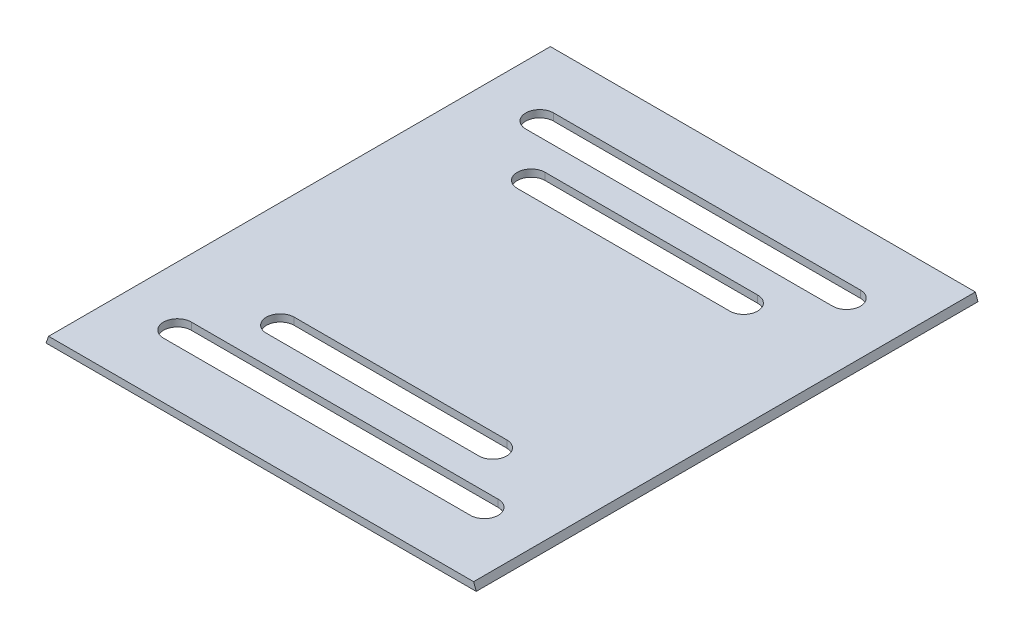
SolidWorks part; units mm, degrees
ref_plane "Front Plane" through (0, 0, 0) normal (0, 0, 1) x (1, 0, 0)
ref_plane "Top Plane" through (0, 0, 0) normal (0, 1, 0) x (1, 0, 0)
ref_plane "Right Plane" through (0, 0, 0) normal (1, 0, 0) x (0, 0, -1)
sketch "Sketch1" plane through (0, 0, 0) normal (0, 0, 1) x (1, 0, 0)
  line L3 (-79.7983, 0.2182) -> (-80.7023, -2.2654)
  line L4 (-80.7023, -2.2654) -> (73.6358, -2.2654)
  line L5 (73.6358, -2.2654) -> (72.7318, 0.2182)
  line L6 (-79.7983, 0.2182) -> (-79.7672, 0.3037)
  line L7 (-79.7672, 0.3037) -> (72.5419, 0.3037)
  line L8 (72.7318, 0.2182) -> (72.7007, 0.3037)
  line L9 (72.7007, 0.3037) -> (72.5419, 0.3037)
extrude "Boss-Extrude1" add sketch "Sketch1" against normal blind 180
sketch "Sketch2" plane through (0, 0.3037, 0) normal (0, 1, 0) x (1, 0, 0)
  line L0 (-3.5332, 180) -> (-3.5332, 0) construction
  line L1 (72.7007, 180) -> (-79.7672, 180) construction
  line L2 (72.7007, 0) -> (-79.7672, 0) construction
  line L3 (-79.7672, 90) -> (72.7007, 90) construction
  line L4 (-79.7672, 180) -> (-79.7672, 0) construction
  line L5 (72.7007, 180) -> (72.7007, 0) construction
  line L6 (-3.5332, 90) -> (-79.7672, 0) construction
  line L7 (-3.5332, 90) -> (72.7007, 0) construction
  line L8 (-41.6502, 50) -> (34.5837, 50)
  line L9 (-41.6502, 40) -> (34.5837, 40)
  line L10 (-56.9956, 30.0246) -> (51.5038, 30.0246)
  line L11 (-58.5703, 20.0246) -> (51.5038, 20.0246)
  line L12 (-56.9956, 30.0246) -> (-58.5703, 30.0246)
  line L13 (-56.9956, 149.9754) -> (-58.5703, 149.9754)
  line L14 (-58.5703, 159.9754) -> (51.5038, 159.9754)
  line L15 (-56.9956, 149.9754) -> (51.5038, 149.9754)
  line L16 (-41.6502, 140) -> (34.5837, 140)
  line L17 (-41.6502, 130) -> (34.5837, 130)
  arc A0 (-41.6502, 50) -> (-41.6502, 40) centre (-41.6502, 45) ccw
  arc A1 (34.5837, 40) -> (34.5837, 50) centre (34.5837, 45) ccw
  arc A2 (-58.5703, 30.0246) -> (-58.5703, 20.0246) centre (-58.5703, 25.0246) ccw
  arc A3 (51.5038, 20.0246) -> (51.5038, 30.0246) centre (51.5038, 25.0246) ccw
  arc A4 (51.5038, 159.9754) -> (51.5038, 149.9754) centre (51.5038, 154.9754) cw
  arc A5 (-58.5703, 149.9754) -> (-58.5703, 159.9754) centre (-58.5703, 154.9754) cw
  arc A6 (34.5837, 140) -> (34.5837, 130) centre (34.5837, 135) cw
  arc A7 (-41.6502, 130) -> (-41.6502, 140) centre (-41.6502, 135) cw
  dimension "D1" = 10
  dimension "D2" = 10
  dimension "D3" = 10
  dimension "D4" = 10
extrude "Cut-Extrude1" cut sketch "Sketch2" against normal blind 3
